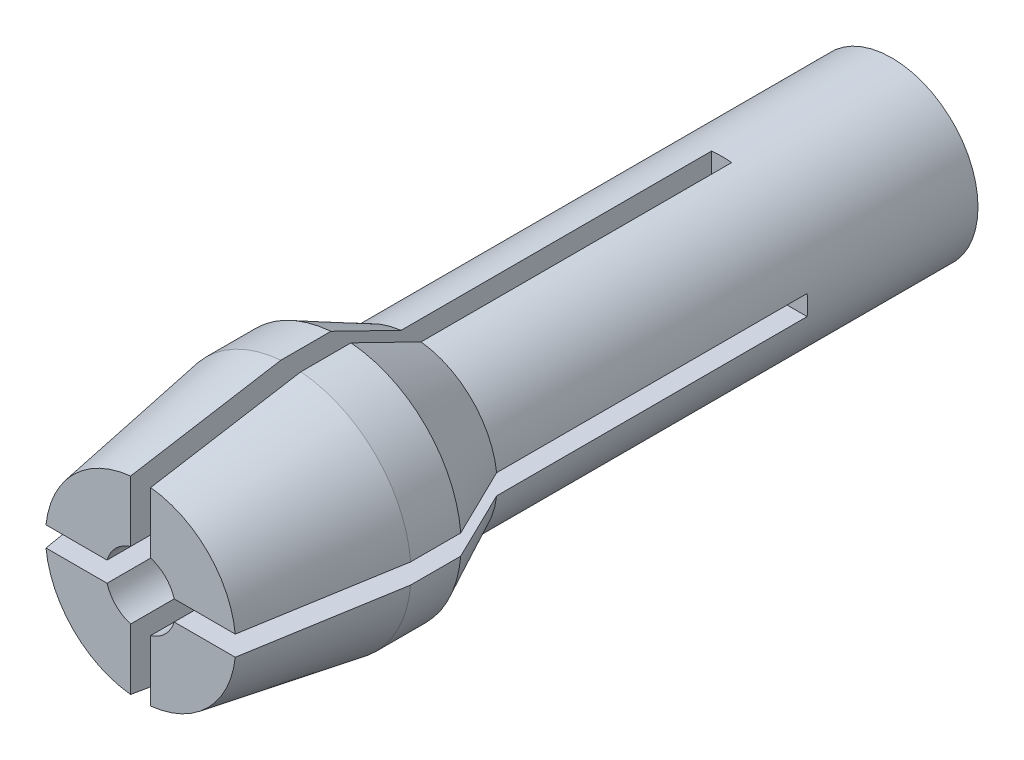
SolidWorks part; units mm, degrees
ref_plane "Front Plane" through (0, 0, 0) normal (0, 0, 1) x (1, 0, 0)
ref_plane "Top Plane" through (0, 0, 0) normal (0, 1, 0) x (1, 0, 0)
ref_plane "Right Plane" through (0, 0, 0) normal (1, 0, 0) x (0, 0, -1)
sketch "Sketch1" plane through (0, 0, 0) normal (0, 0, 1) x (1, 0, 0)
  circle A0 centre (0, 0) radius 2.15
  circle A1 centre (0, 0) radius 0.875
  dimension "D1" = 4.3
  dimension "D2" = 1.75
extrude "Boss-Extrude1" add sketch "Sketch1" along normal blind 12
sketch "Sketch2" plane through (0, 0, 12) normal (0, 0, 1) x (1, 0, 0)
  circle A0 centre (0, 0) radius 3
  circle A1 centre (0, 0) radius 0.8743
  dimension "D1" = 6
extrude "Boss-Extrude2" add sketch "Sketch2" along normal blind 6.75
sketch "Sketch3" plane through (0, 0, 0) normal (0, 1, 0) x (1, 0, 0)
  line L0 (2.15, -12) -> (3, -13.75)
  line L1 (2.15, -12) -> (2.15, 0) construction
  line L2 (3, -12) -> (-3, -12) construction
  line L3 (3, -18.75) -> (3, -12) construction
  line L4 (2.15, -12) -> (3.1266, -11.3717)
  line L5 (3.1266, -11.3717) -> (4.2549, -13.1254)
  line L6 (4.2549, -13.1254) -> (3, -13.75)
  line L7 (0, -18.75) -> (2.375, -18.75) construction
  line L8 (-3, -18.75) -> (3, -18.75) construction
  line L9 (2.375, -18.75) -> (3, -15)
  line L10 (3, -15) -> (5.7518, -16.4218)
  line L11 (5.7518, -16.4218) -> (4.2549, -20.9396)
  line L12 (4.2549, -20.9396) -> (2.375, -18.75)
  dimension "D1" = 1.75
  dimension "D2" = 2.375
  dimension "D3" = 3.75
sketch3d "3DSketch1"
  line L0 (0, 0, 0) -> (0, 0, 18.75) construction
revolve "Cut-Revolve1" cut sketch "Sketch3" angle 360 about L0
sketch "Sketch4" plane through (0, 0, 18.75) normal (0, 0, 1) x (1, 0, 0)
  line L0 (0, 0) -> (0, 3.3408) construction
  line L1 (0, 3.3408) -> (-0.25, 3.3408)
  line L2 (-0.25, 3.3408) -> (-0.25, 0.4648)
  line L3 (-0.25, 0.4648) -> (0.25, 0.4648)
  line L4 (0.25, 0.4648) -> (0.25, 3.3408)
  line L5 (0.25, 3.3408) -> (0, 3.3408)
  line L6 (3.3408, 0) -> (3.3408, 0.25)
  line L7 (3.3408, 0.25) -> (0.4648, 0.25)
  line L8 (0.4648, 0.25) -> (0.4648, -0.25)
  line L9 (0.4648, -0.25) -> (3.3408, -0.25)
  line L10 (3.3408, -0.25) -> (3.3408, 0)
  line L11 (0, 0) -> (3.3408, 0) construction
  line L12 (0, -3.3408) -> (0.25, -3.3408)
  line L13 (0.25, -3.3408) -> (0.25, -0.4648)
  line L14 (0.25, -0.4648) -> (-0.25, -0.4648)
  line L15 (-0.25, -0.4648) -> (-0.25, -3.3408)
  line L16 (-0.25, -3.3408) -> (0, -3.3408)
  line L17 (0, 0) -> (0, -3.3408) construction
  line L18 (-3.3408, 0) -> (-3.3408, -0.25)
  line L19 (-3.3408, -0.25) -> (-0.4648, -0.25)
  line L20 (-0.4648, -0.25) -> (-0.4648, 0.25)
  line L21 (-0.4648, 0.25) -> (-3.3408, 0.25)
  line L22 (-3.3408, 0.25) -> (-3.3408, 0)
  line L23 (0, 0) -> (-3.3408, 0) construction
  point P25 (0, 0)
  dimension "D1" = 0.25
  dimension "D2" = 0.25
  dimension "D3" = 4
extrude "Cut-Extrude1" cut sketch "Sketch4" against normal blind 14.5
equation "\"D2@Sketch3\"=4.75/2"
